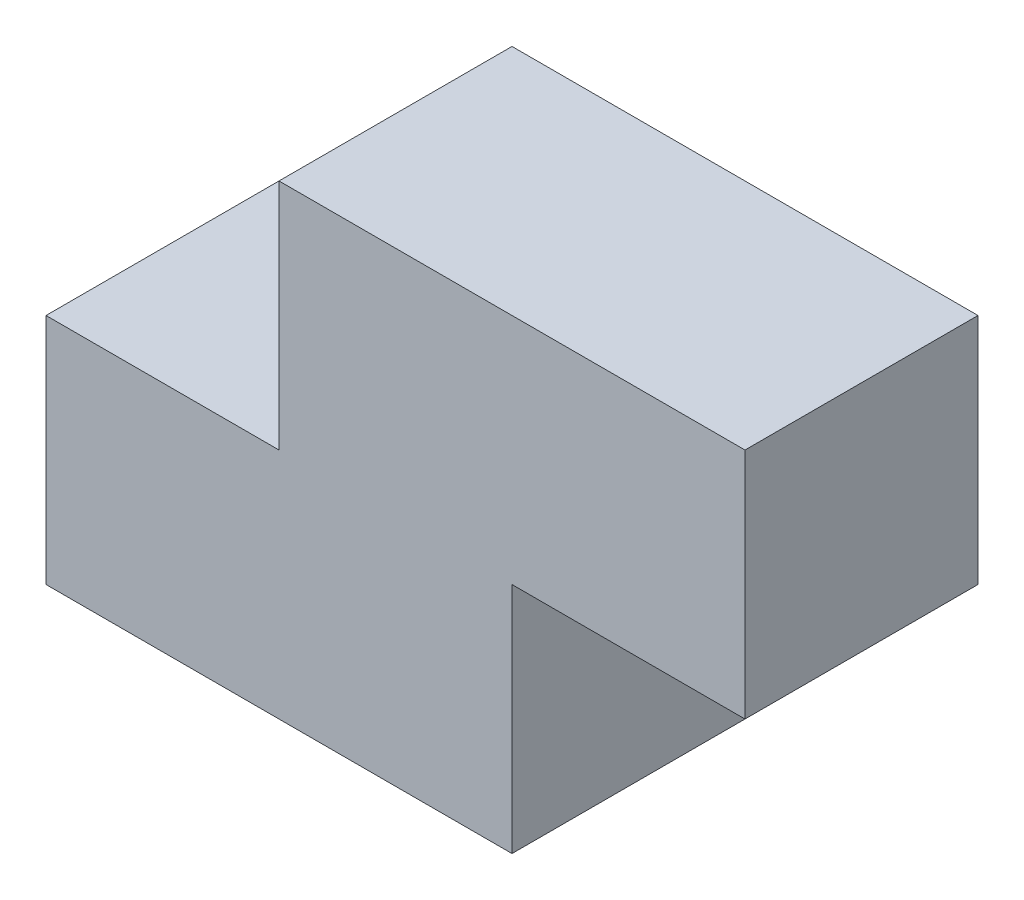
SolidWorks part; units mm, degrees
material "AISI 1020 Steel, Cold Rolled"
ref_plane "Front Plane" through (0, 0, 0) normal (0, 0, 1) x (1, 0, 0)
ref_plane "Top Plane" through (0, 0, 0) normal (0, 1, 0) x (1, 0, 0)
ref_plane "Right Plane" through (0, 0, 0) normal (1, 0, 0) x (0, 0, -1)
sketch "Sketch1" plane through (0, 0, 0) normal (0, 0, 1) x (1, 0, 0)
  line L0 (0, 0) -> (60, 0)
  line L1 (60, 0) -> (60, 30)
  line L2 (60, 30) -> (90, 30)
  line L3 (90, 30) -> (90, 60)
  line L4 (90, 60) -> (30, 60)
  line L5 (30, 60) -> (30, 30)
  line L6 (30, 30) -> (0, 30)
  line L7 (0, 30) -> (0, 0)
  dimension "D1" = 60
  dimension "D2" = 30
  dimension "D3" = 30
  dimension "D4" = 60
  dimension "D5" = 30
  dimension "D6" = 30
extrude "Boss-Extrude1" add sketch "Sketch1" along normal blind 30
